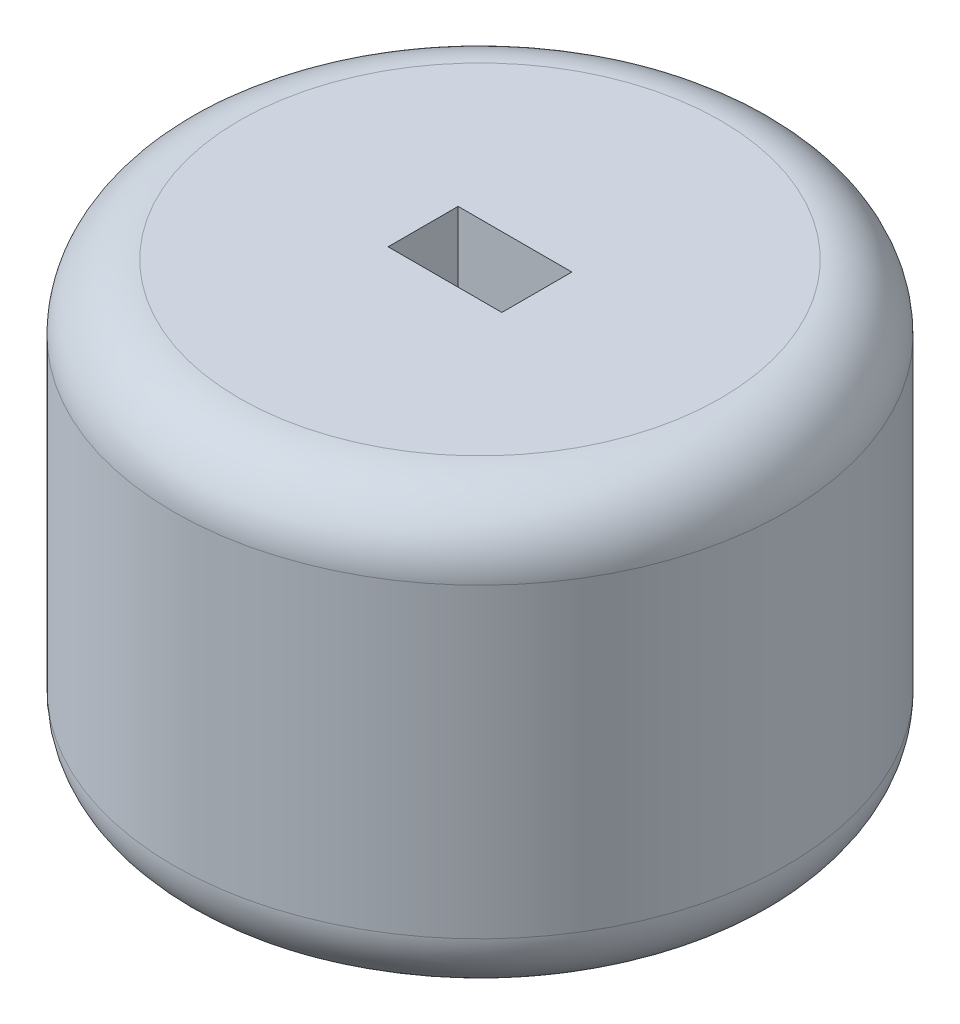
SolidWorks part; units mm, degrees
ref_plane "Front Plane" through (0, 0, 0) normal (0, 0, 1) x (1, 0, 0)
ref_plane "Top Plane" through (0, 0, 0) normal (0, 1, 0) x (1, 0, 0)
ref_plane "Right Plane" through (0, 0, 0) normal (1, 0, 0) x (0, 0, -1)
sketch "Sketch2" plane through (0, 0, 0) normal (0, 1, 0) x (1, 0, 0)
  circle A0 centre (0, 0) radius 14
  dimension "D1" = 28
extrude "Boss-Extrude1" add sketch "Sketch2" along normal blind 20
fillet "Fillet1" radius 3 2 edges at (0, 0, 14) (0, 20, 14)
sketch "Sketch3" plane through (0, 0, 0) normal (0, -1, 0) x (1, 0, 0)
  line L1 (-2.6, -1.6) -> (2.6, -1.6)
  line L2 (-2.6, -1.6) -> (-2.6, 1.6)
  line L3 (-2.6, 1.6) -> (2.6, 1.6)
  line L4 (2.6, -1.6) -> (2.6, 1.6)
  line L5 (0, 1.6) -> (0, -1.6) construction
  line L6 (-2.6, 0) -> (2.6, 0) construction
  point P0 (0, 0)
  dimension "D1" = 3.2
  dimension "D2" = 5.2
extrude "Cut-Extrude1" cut sketch "Sketch3" against normal through all
